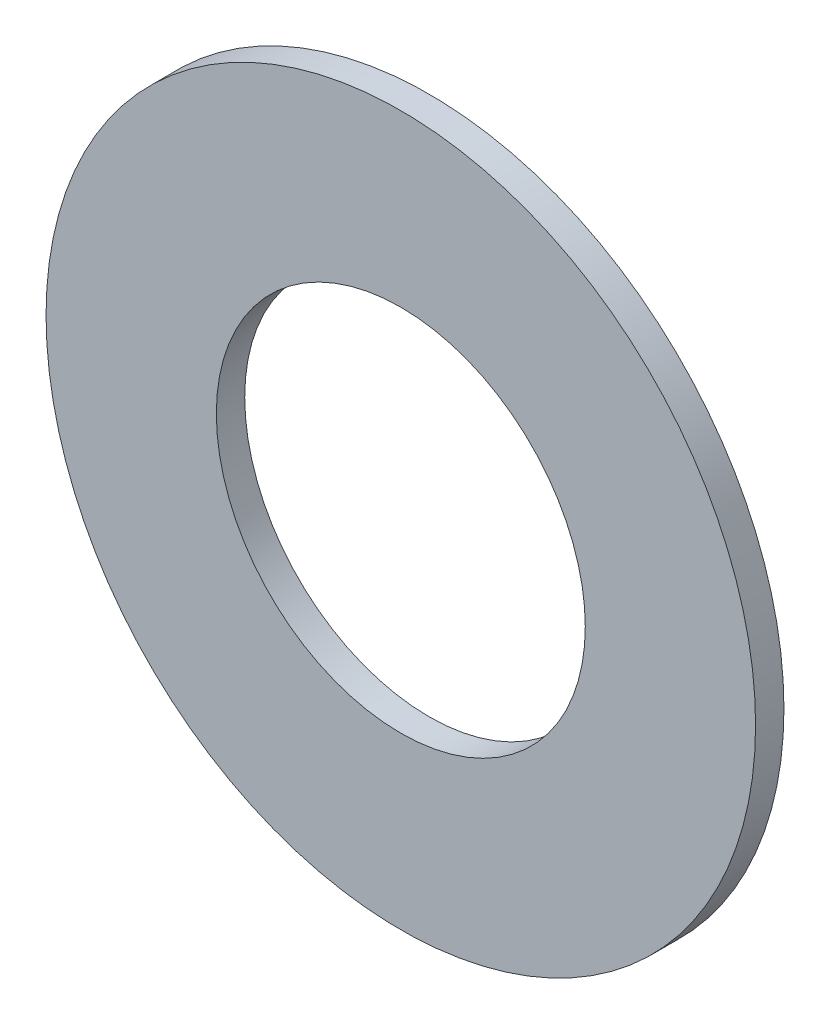
SolidWorks part; units mm, degrees
ref_plane "Front Plane" through (0, 0, 0) normal (0, 0, 1) x (1, 0, 0)
ref_plane "Top Plane" through (0, 0, 0) normal (0, 1, 0) x (1, 0, 0)
ref_plane "Right Plane" through (0, 0, 0) normal (1, 0, 0) x (0, 0, -1)
sketch "Sketch1" plane through (0, 0, 0) normal (0, 0, 1) x (1, 0, 0)
  circle A0 centre (0, 0) radius 3.302
  circle A1 centre (0, 0) radius 6.35
  point P4 (-3.302, 0)
  dimension "ID" = 6.604
  dimension "OD" = 12.7
extrude "Extrude1" add sketch "Sketch1" against normal blind 0.508
